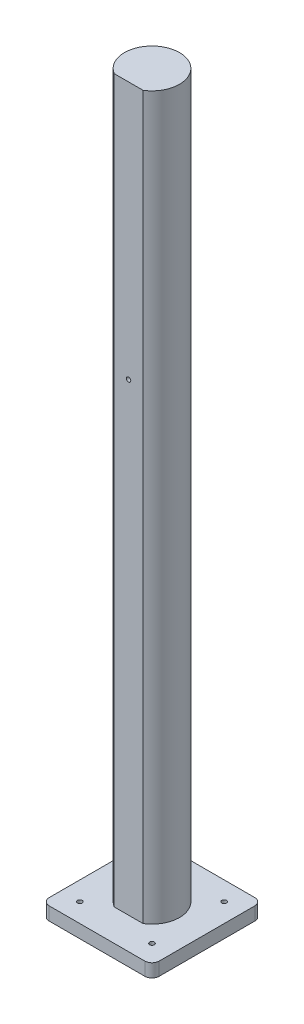
SolidWorks part; units mm, degrees
ref_plane "Front Plane" through (0, 0, 0) normal (0, 0, 1) x (1, 0, 0)
ref_plane "Top Plane" through (0, 0, 0) normal (0, 1, 0) x (1, 0, 0)
ref_plane "Right Plane" through (0, 0, 0) normal (1, 0, 0) x (0, 0, -1)
sketch "Sketch3" plane through (0, 0, 0) normal (0, 1, 0) x (1, 0, 0)
  line L0 (-10, -16.2143) -> (10, -16.2143)
  arc A0 (10, -16.2143) -> (-10, -16.2143) centre (0, 0) ccw
  dimension "D1" = 38.1
  dimension "D2" = 20
extrude "Boss-Extrude1" add sketch "Sketch3" along normal blind 500
sketch "Sketch5" plane through (0, 0, 16.2143) normal (0, 0, 1) x (1, 0, 0)
  line L0 (-10, 0) -> (10, 0) construction
  circle A0 centre (0, 321.4) radius 1.5
  dimension "D1" = 3
  dimension "D2" = 321.4
extrude "Cut-Extrude1" cut sketch "Sketch5" against normal blind 5
sketch "Sketch6" plane through (0, 0, 0) normal (0, -1, 0) x (1, 0, 0)
  line L1 (-38.1, -38.1) -> (38.1, -38.1)
  line L2 (-38.1, -38.1) -> (-38.1, 38.1)
  line L3 (-38.1, 38.1) -> (38.1, 38.1)
  line L4 (38.1, -38.1) -> (38.1, 38.1)
  line L5 (-38.1, -38.1) -> (38.1, 38.1) construction
  line L6 (-38.1, 38.1) -> (38.1, -38.1) construction
  point P0 (0, 0)
  dimension "D1" = 76.2
extrude "Boss-Extrude2" add sketch "Sketch6" along normal blind 9.144
sketch "Sketch7" plane through (0, -9.144, 0) normal (0, -1, 0) x (1, 0, 0)
  line L1 (-25, -25) -> (25, -25) construction
  line L2 (-25, -25) -> (-25, 25) construction
  line L3 (-25, 25) -> (25, 25) construction
  line L4 (25, -25) -> (25, 25) construction
  line L5 (-25, -25) -> (25, 25) construction
  line L6 (-25, 25) -> (25, -25) construction
  circle A0 centre (-25, 25) radius 1.65
  circle A1 centre (25, 25) radius 1.65
  circle A2 centre (25, -25) radius 1.65
  circle A3 centre (-25, -25) radius 1.65
  point P3 (0, 0)
  dimension "D1" = 3.3
  dimension "D2" = 50
extrude "Cut-Extrude2" cut sketch "Sketch7" against normal up to surface (9.144 mm away) up to face at (0, 0, 0)
fillet "Fillet1" radius 5 4 edges at (-38.1, -4.572, 38.1) (-38.1, -4.572, -38.1) (38.1, -4.572, -38.1) (38.1, -4.572, 38.1)
